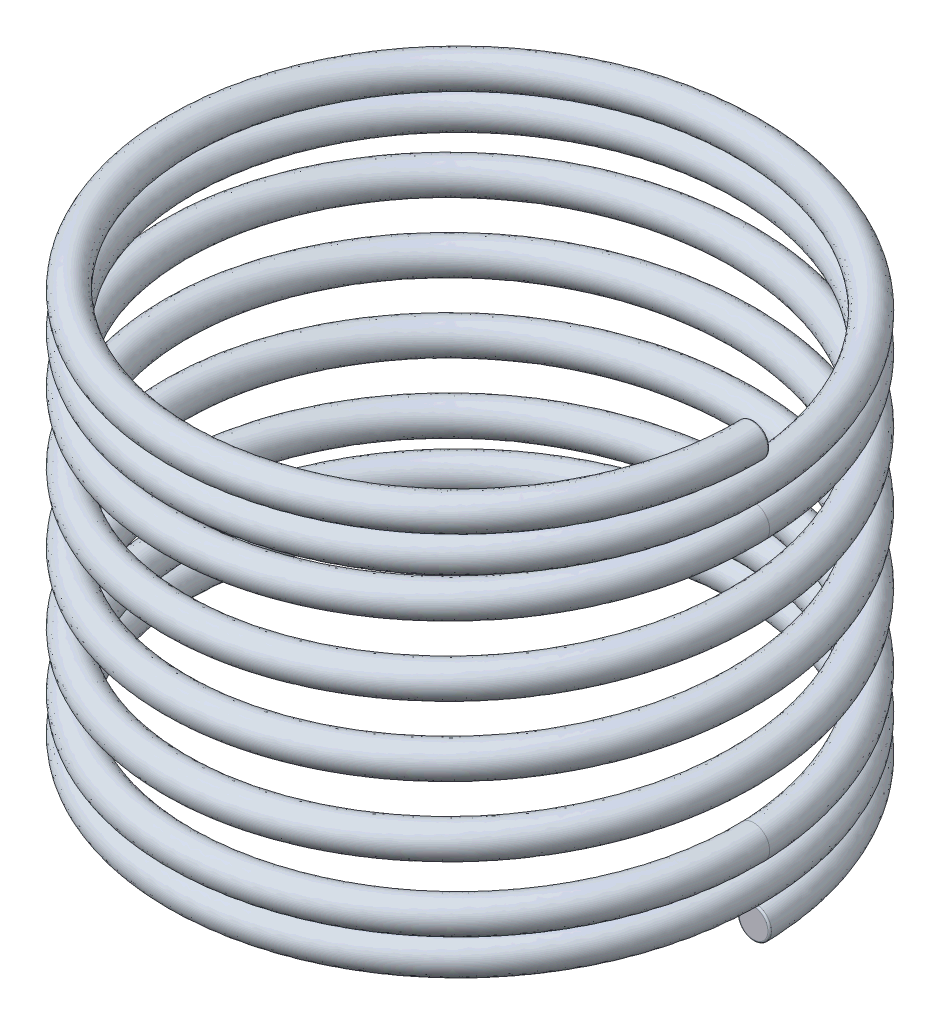
SolidWorks part; units mm, degrees
material "Alloy Steel"
ref_plane "Front Plane" through (0, 0, 0) normal (0, 0, 1) x (1, 0, 0)
ref_plane "Top Plane" through (0, 0, 0) normal (0, 1, 0) x (1, 0, 0)
ref_plane "Right Plane" through (0, 0, 0) normal (1, 0, 0) x (0, 0, -1)
sketch "Sketch4" plane through (0, 0, 0) normal (0, 1, 0) x (1, 0, 0)
  circle A0 centre (0, 0) radius 4
  dimension "D1" = 8
curve "Helix/Spiral2" pitch 0.5 height 1 turns 2
sketch "Sketch8" plane through (0, 0, 0) normal (0, 0, 1) x (1, 0, 0)
  line L0 (0, 0) -> (0, -1) construction
  line L1 (0, -1) -> (0.8144, -1) construction
  dimension "D1" = 1
sketch "Sketch9" plane through (0, 0, 0) normal (1, 0, 0) x (0, 0, -1)
  line L0 (0, -1) -> (-0.3019, -1) construction
  line L1 (0, 0) -> (0, -1) construction
ref_plane "Plane2" through (0, -1, 0) normal (0, -1, 0) x (-1, 0, 0)
sketch "Sketch10" plane through (0, -1, 0) normal (0, -1, 0) x (-1, 0, 0)
  circle A0 centre (0, 0) radius 4
  dimension "D1" = 8
curve "Helix/Spiral4" pitch 0.9801 height 3.9206 turns 4
sketch "Sketch11" plane through (0, 0, 0) normal (0, 0, 1) x (1, 0, 0)
  line L0 (0, -1) -> (0, -4.9206) construction
  line L1 (0, -4.9206) -> (0.5594, -4.9206) construction
  dimension "D1" = 3.9206
sketch "Sketch12" plane through (0, 0, 0) normal (1, 0, 0) x (0, 0, -1)
  line L0 (0, -4.9206) -> (-0.7004, -4.9206) construction
  line L1 (0, -1) -> (0, -4.9206) construction
  spline S0 degree 3 poles (0, -1) (-0.5202, -1.0203) (-1.5721, -1.0613) (-2.9017, -1.1225) (-3.7918, -1.1838) (-4.1041, -1.245) (-3.7917, -1.3063) (-2.9021, -1.3676) (-1.5706, -1.4288) (0, -1.4901) (1.5706, -1.5513) (2.9021, -1.6126) (3.7917, -1.6739) (4.1041, -1.7351) (3.7917, -1.7964) (2.9021, -1.8576) (1.5706, -1.9189) (0, -1.9801) (-1.5706, -2.0414) (-2.9021, -2.1027) (-3.7917, -2.1639) (-4.1041, -2.2252) (-3.7917, -2.2864) (-2.9021, -2.3477) (-1.5706, -2.409) (0, -2.4702) (1.5706, -2.5315) (2.9021, -2.5927) (3.7917, -2.654) (4.1041, -2.7153) (3.7917, -2.7765) (2.9021, -2.8378) (1.5706, -2.899) (0, -2.9603) (-1.5706, -3.0216) (-2.9021, -3.0828) (-3.7917, -3.1441) (-4.1041, -3.2053) (-3.7917, -3.2666) (-2.9021, -3.3279) (-1.5706, -3.3891) (0, -3.4504) (1.5706, -3.5116) (2.9021, -3.5729) (3.7917, -3.6342) (4.1041, -3.6954) (3.7917, -3.7567) (2.9021, -3.8179) (1.5706, -3.8792) (0, -3.9405) (-1.5706, -4.0017) (-2.9021, -4.063) (-3.7917, -4.1242) (-4.1041, -4.1855) (-3.7917, -4.2467) (-2.9021, -4.308) (-1.5706, -4.3693) (0, -4.4305) (1.5706, -4.4918) (2.9021, -4.553) (3.7917, -4.6143) (4.1041, -4.6756) (3.7918, -4.7368) (2.9017, -4.7981) (1.5721, -4.8593) (0.5202, -4.9003) (0, -4.9206) knots 0 0 0 0 0.015625 0.03125 0.046875 0.0625 0.078125 0.09375 0.109375 0.125 0.140625 0.15625 0.171875 0.1875 0.203125 0.21875 0.234375 0.25 0.265625 0.28125 0.296875 0.3125 0.328125 0.34375 0.359375 0.375 0.390625 0.40625 0.421875 0.4375 0.453125 0.46875 0.484375 0.5 0.515625 0.53125 0.546875 0.5625 0.578125 0.59375 0.609375 0.625 0.640625 0.65625 0.671875 0.6875 0.703125 0.71875 0.734375 0.75 0.765625 0.78125 0.796875 0.8125 0.828125 0.84375 0.859375 0.875 0.890625 0.90625 0.921875 0.9375 0.953125 0.96875 0.984375 1 1 1 1 construction
ref_plane "Plane3" through (0, -4.9206, 0) normal (0, -1, 0) x (-1, 0, 0)
sketch "Sketch13" plane through (0, -4.9206, 0) normal (0, -1, 0) x (-1, 0, 0)
  circle A0 centre (0, 0) radius 4
  dimension "D1" = 8
curve "Helix/Spiral5" pitch 0.5 height 1 turns 2
sketch "Sketch14" plane through (0, 0, 0) normal (0, 0, 1) x (1, 0, 0)
  circle A0 centre (4, 0) radius 0.2275
  spline S0 degree 3 poles (4, 0) (4, -0.0103) (3.7917, -0.0313) (2.9021, -0.0625) (1.5706, -0.0938) (0, -0.125) (-1.5706, -0.1563) (-2.9021, -0.1875) (-3.7917, -0.2188) (-4.1041, -0.25) (-3.7917, -0.2813) (-2.9021, -0.3125) (-1.5706, -0.3438) (0, -0.375) (1.5706, -0.4063) (2.9021, -0.4375) (3.7917, -0.4688) (4.1041, -0.5) (3.7917, -0.5312) (2.9021, -0.5625) (1.5706, -0.5937) (0, -0.625) (-1.5706, -0.6562) (-2.9021, -0.6875) (-3.7917, -0.7187) (-4.1041, -0.75) (-3.7917, -0.7812) (-2.9021, -0.8125) (-1.5706, -0.8437) (0, -0.875) (1.5706, -0.9062) (2.9021, -0.9375) (3.7917, -0.9687) (4, -0.9897) (4, -1) knots 0 0 0 0 0.03125 0.0625 0.09375 0.125 0.15625 0.1875 0.21875 0.25 0.28125 0.3125 0.34375 0.375 0.40625 0.4375 0.46875 0.5 0.53125 0.5625 0.59375 0.625 0.65625 0.6875 0.71875 0.75 0.78125 0.8125 0.84375 0.875 0.90625 0.9375 0.96875 1 1 1 1 construction
  dimension "D1" = 0.455
sweep "Sweep1" add profiles "Sketch14" path "Helix/Spiral2"
sketch "Sketch16" plane through (0, 0, 0) normal (0, 0, 1) x (1, 0, 0)
  circle A0 centre (4, -1) radius 0.2275
  spline S0 degree 3 poles (4, -1) (4, -1.0203) (3.7917, -1.0613) (2.9021, -1.1225) (1.5706, -1.1838) (0, -1.245) (-1.5706, -1.3063) (-2.9021, -1.3676) (-3.7917, -1.4288) (-4.1041, -1.4901) (-3.7917, -1.5513) (-2.9021, -1.6126) (-1.5706, -1.6739) (0, -1.7351) (1.5706, -1.7964) (2.9021, -1.8576) (3.7917, -1.9189) (4.1041, -1.9801) (3.7917, -2.0414) (2.9021, -2.1027) (1.5706, -2.1639) (0, -2.2252) (-1.5706, -2.2864) (-2.9021, -2.3477) (-3.7917, -2.409) (-4.1041, -2.4702) (-3.7917, -2.5315) (-2.9021, -2.5927) (-1.5706, -2.654) (0, -2.7153) (1.5706, -2.7765) (2.9021, -2.8378) (3.7917, -2.899) (4.1041, -2.9603) (3.7917, -3.0216) (2.9021, -3.0828) (1.5706, -3.1441) (0, -3.2053) (-1.5706, -3.2666) (-2.9021, -3.3279) (-3.7917, -3.3891) (-4.1041, -3.4504) (-3.7917, -3.5116) (-2.9021, -3.5729) (-1.5706, -3.6342) (0, -3.6954) (1.5706, -3.7567) (2.9021, -3.8179) (3.7917, -3.8792) (4.1041, -3.9405) (3.7917, -4.0017) (2.9021, -4.063) (1.5706, -4.1242) (0, -4.1855) (-1.5706, -4.2467) (-2.9021, -4.308) (-3.7917, -4.3693) (-4.1041, -4.4305) (-3.7917, -4.4918) (-2.9021, -4.553) (-1.5706, -4.6143) (0, -4.6756) (1.5706, -4.7368) (2.9021, -4.7981) (3.7917, -4.8593) (4, -4.9003) (4, -4.9206) knots 0 0 0 0 0.015625 0.03125 0.046875 0.0625 0.078125 0.09375 0.109375 0.125 0.140625 0.15625 0.171875 0.1875 0.203125 0.21875 0.234375 0.25 0.265625 0.28125 0.296875 0.3125 0.328125 0.34375 0.359375 0.375 0.390625 0.40625 0.421875 0.4375 0.453125 0.46875 0.484375 0.5 0.515625 0.53125 0.546875 0.5625 0.578125 0.59375 0.609375 0.625 0.640625 0.65625 0.671875 0.6875 0.703125 0.71875 0.734375 0.75 0.765625 0.78125 0.796875 0.8125 0.828125 0.84375 0.859375 0.875 0.890625 0.90625 0.921875 0.9375 0.953125 0.96875 0.984375 1 1 1 1 construction
sweep "Sweep2" add profiles "Sketch16" path "Helix/Spiral4"
sketch "Sketch17" plane through (0, 0, 0) normal (0, 0, 1) x (1, 0, 0)
  circle A0 centre (4, -4.9206) radius 0.2275
  spline S0 degree 3 poles (4, -4.9206) (4, -4.9309) (3.7917, -4.9519) (2.9021, -4.9831) (1.5706, -5.0144) (0, -5.0456) (-1.5706, -5.0769) (-2.9021, -5.1081) (-3.7917, -5.1394) (-4.1041, -5.1706) (-3.7917, -5.2019) (-2.9021, -5.2331) (-1.5706, -5.2644) (0, -5.2956) (1.5706, -5.3269) (2.9021, -5.3581) (3.7917, -5.3894) (4.1041, -5.4206) (3.7917, -5.4518) (2.9021, -5.4831) (1.5706, -5.5143) (0, -5.5456) (-1.5706, -5.5768) (-2.9021, -5.6081) (-3.7917, -5.6393) (-4.1041, -5.6706) (-3.7917, -5.7018) (-2.9021, -5.7331) (-1.5706, -5.7643) (0, -5.7956) (1.5706, -5.8268) (2.9021, -5.8581) (3.7917, -5.8893) (4, -5.9103) (4, -5.9206) knots 0 0 0 0 0.03125 0.0625 0.09375 0.125 0.15625 0.1875 0.21875 0.25 0.28125 0.3125 0.34375 0.375 0.40625 0.4375 0.46875 0.5 0.53125 0.5625 0.59375 0.625 0.65625 0.6875 0.71875 0.75 0.78125 0.8125 0.84375 0.875 0.90625 0.9375 0.96875 1 1 1 1 construction
sweep "Sweep3" add profiles "Sketch17" path "Helix/Spiral5"
fillet "Fillet2" radius 0.025 1 edges at (3.7725, -5.9206, 0)
fillet "Fillet3" radius 0.025 1 edges at (4.2275, 0, 0)
